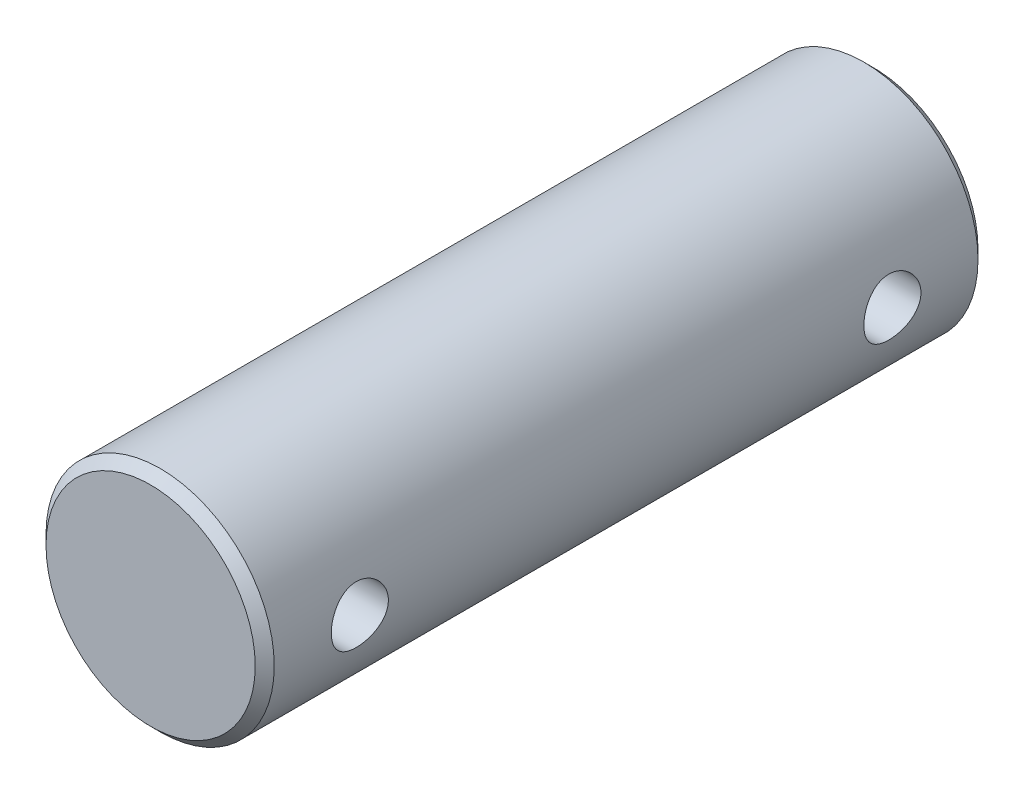
SolidWorks part; units mm, degrees
material "Stainless Steel (ferritic)"
ref_plane "Front Plane" through (0, 0, 0) normal (0, 0, 1) x (1, 0, 0)
ref_plane "Top Plane" through (0, 0, 0) normal (0, 1, 0) x (1, 0, 0)
ref_plane "Right Plane" through (0, 0, 0) normal (1, 0, 0) x (0, 0, -1)
sketch "Sketch3" plane through (0, 0, 0) normal (0, 0, 1) x (1, 0, 0)
  circle A0 centre (0, 0) radius 3
  dimension "D1" = 6
extrude "Boss-Extrude1" add sketch "Sketch3" along normal blind 19
sketch "Sketch4" plane through (0, 0, 0) normal (1, 0, 0) x (0, 0, -1)
  line L0 (-19, 3) -> (-19, -3) construction
  line L1 (0, 3) -> (-19, 3) construction
  circle A0 centre (-2.5, 0) radius 0.75
  circle A1 centre (-16.5, 0) radius 0.75
  dimension "D1" = 1.5
  dimension "D2" = 1.5
  dimension "D3" = 2.5
  dimension "D4" = 3
  dimension "2.5" = 2.5
  dimension "D5" = 3
extrude "Cut-Extrude1" cut sketch "Sketch4" against normal through all both and the other way through all
chamfer "Chamfer1" distance 0.25 angle 45 2 edges at (3, 0, 0) (3, 0, 19)
